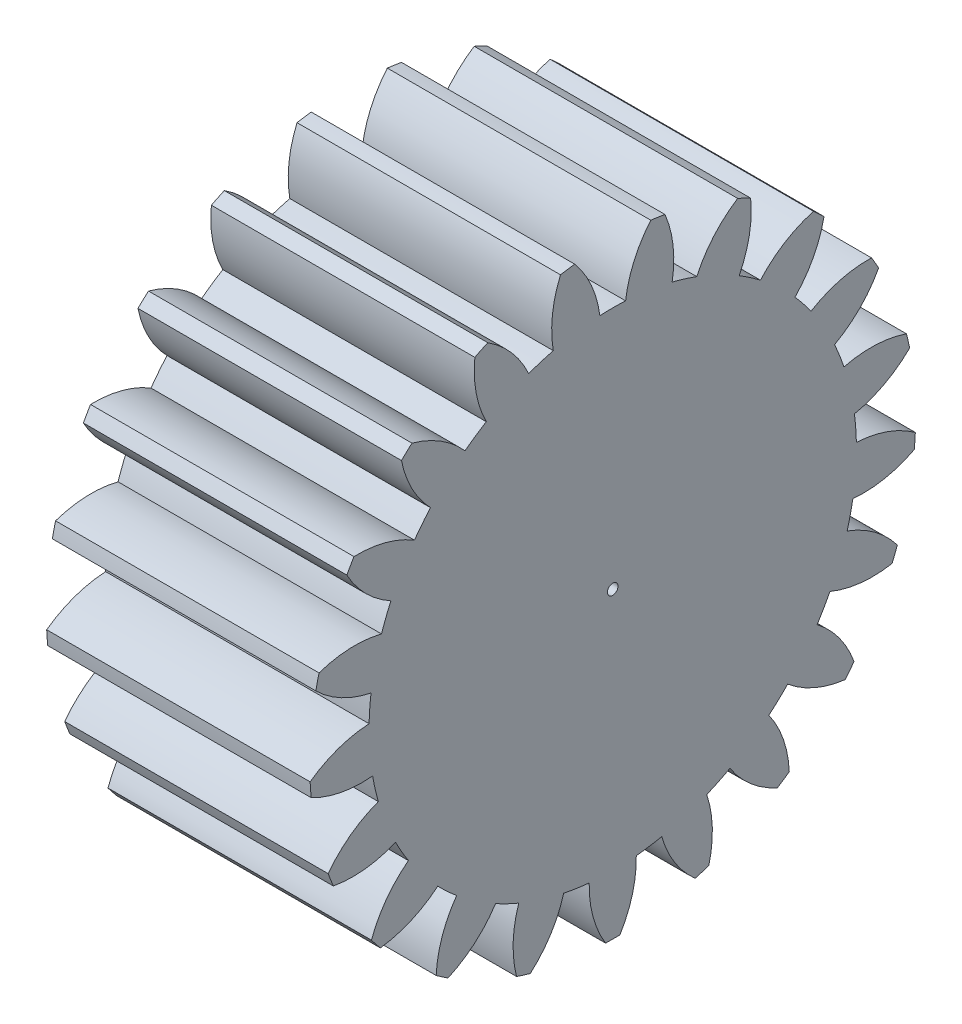
SolidWorks part; units mm, degrees
ref_plane "Plane1" through (0, 0, 0) normal (0, 0, 1) x (1, 0, 0)
ref_plane "Plane2" through (0, 0, 0) normal (0, 1, 0) x (1, 0, 0)
ref_plane "Plane3" through (0, 0, 0) normal (1, 0, 0) x (0, 0, -1)
sketch "HoldingSke" plane through (0, 0, 0) normal (0, 1, 0) x (1, 0, 0)
  line L0 (0, 0) -> (0.4668, -0.1792)
  line L1 (-15, 0) -> (100, 0) construction
  line L2 (0, 0) -> (-2.1039, 2.3779)
  line L3 (0, 0) -> (-11.863, 4.5341)
  line L4 (0, 0) -> (8.0624, 3.0949)
  line L5 (0, 0) -> (-46.8476, -17.4728)
  line L6 (0, 0) -> (-16.5793, -11.1861)
  line L7 (-2.1039, 2.3779) -> (8.6586, 51.2059)
  line L8 (-76.2, 54.61) -> (-76.1, 54.61)
  line L9 (-71.009, 38.7566) -> (-53.1078, 45.2721)
  line L10 (-76.2, 71.12) -> (104.1128, 71.12)
  line L11 (0, 0) -> (-20, 0)
  line L12 (-76.2, 101.6) -> (-76.133, 101.6)
  line L13 (24.9733, 27.94) -> (52.9518, 28.4284)
  line L14 (24.9733, 27.94) -> (24.9743, 27.94)
  line L15 (24.9733, 27.94) -> (100.4006, 29.5858)
  line L16 (-63.627, -2) -> (-12.827, -2)
  circle A0 centre (0, 0) radius 0.4
  circle A1 centre (0, 0) radius 18.499
  circle A2 centre (0, 0) radius 37.5
  circle A3 centre (0, 0) radius 0.4
  dimension "MHD" = 36.998
  dimension "Hub_dia" = 75
  dimension "Bore" = 0.8
  dimension "MBD" = 0.8
  dimension "Num_teeth" = 21
  dimension "Pitch" = 0.5
  dimension "Overall_len" = 50
  dimension "Show_teeth" = 21
  dimension "Thickness" = 20
  dimension "OAL" = 50.0001
  dimension "T_dim" = 0.1
  dimension "Ap" = 20
  dimension "H" = 19.05
  dimension "Pitch_radius" = 180.3128
  dimension "Width" = 20
  dimension "Backlash" = 0.067
  dimension "Addendum_fac" = 1
  dimension "Dedendum_fac" = 1.25
  dimension "Clearance_fac" = 0.25
  dimension "Dedendum_add" = 0.001
  dimension "Module" = 2
sketch "BasProSke" plane through (0, 0, 0) normal (0, 1, 0) x (1, 0, 0)
  line L0 (-10, 0) -> (60, 0) construction
  line L1 (0, 0) -> (0, 23)
  line L2 (0, 0) -> (20, 0)
  line L3 (20, 0) -> (20, 23)
  line L4 (20, 23) -> (0, 23)
  dimension "Thickness" = 20
  dimension "Diameter" = 46
revolve "Base-Revolve" add sketch "BasProSke" angle 360 about L0
sketch "TooCutSke" plane through (0, 0, 0) normal (1, 0, 0) x (0, 0, -1)
  line L1 (0, 0) -> (0, 107) construction
  line L2 (0, 0) -> (-1.6865, 20.9322) construction
  line L3 (0, 0) -> (-6.2448, 41.4315) construction
  line L4 (-1.6865, 20.9322) -> (-3.1224, 20.7157) construction
  arc A0 (0.9768, 18.4732) -> (-0.9768, 18.4732) centre (0, 0) ccw
  arc A1 (2.908, 22.841) -> (-2.908, 22.841) centre (0, 0) ccw
  circle A2 centre (0, 0) radius 21 construction
  circle A3 centre (0, 0) radius 19.7335 construction
  arc A4 (-0.9768, 18.4732) -> (-2.908, 22.841) centre (-9.308, 17.4004) ccw
  arc A5 (2.908, 22.841) -> (0.9768, 18.4732) centre (9.308, 17.4004) ccw
  dimension "Root_dia" = 36.998
  dimension "Overcut_dia" = 46.0508
  dimension "Pitch_dia" = 42
  dimension "Base_dia" = 39.4671
  dimension "Flank_rad" = 8.4
  dimension "Half_ang" = 8.571
  dimension "Half_CT" = 1.4521
extrude "ToothCut" cut sketch "TooCutSke" along normal through all
fillet "Breaks" [suppressed] radius 0.04
fillet "RootFillets" [suppressed] radius 0.501
pattern_circular "TeethCuts" count 21 every 17.143 about axis through (-10, 0, 0) along (1, 0, 0) of "ToothCut", "RootFillets", "Breaks"
sketch "HubNeaOneSke" plane through (0, 0, 0) normal (-1, 0, 0) x (0, 0, 1)
  circle A0 centre (0, 0) radius 18.499
  dimension "Diameter" = 36.998
extrude "HubNearOne" [suppressed] add sketch "HubNeaOneSke" along normal blind 30.0001
sketch "HubNeaBotSke" plane through (0, 0, 0) normal (-1, 0, 0) x (0, 0, 1)
  circle A0 centre (0, 0) radius 18.499
  dimension "Diameter" = 36.998
extrude "HubNearBoth" [suppressed] add sketch "HubNeaBotSke" along normal blind 15
ref_plane "FarPln" through (20, 0, 0) normal (1, 0, 0) x (0, 0, -1)
sketch "HubFarSke" plane through (20, 0, 0) normal (1, 0, 0) x (0, 0, -1)
  circle A0 centre (0, 0) radius 18.499
  dimension "Diameter" = 36.998
extrude "HubFar" [suppressed] add sketch "HubFarSke" along normal blind 15
sketch "BorSke" plane through (0, 0, 0) normal (1, 0, 0) x (0, 0, -1)
  circle A0 centre (0, 0) radius 0.4
  dimension "Diameter" = 0.8
extrude "Bore" cut sketch "BorSke" along normal mid plane 100.0001
sketch "KeySke" plane through (0, 0, 0) normal (1, 0, 0) x (0, 0, -1)
  line L0 (-0.05, 0) -> (-0.05, 0.5)
  line L1 (-0.05, 0.5) -> (0.05, 0.5)
  line L2 (0.05, 0.5) -> (0.05, 0)
  line L3 (0, 0) -> (0, 34) construction
  line L4 (-0.05, 0) -> (0.05, 0)
  dimension "Offset" = 0.5
  dimension "Width" = 0.1
extrude "Keyway" [suppressed] cut sketch "KeySke" along normal mid plane 100.0001
pattern_circular "Keyway2" [suppressed] count 2 every 90 about axis through (-10, 0, 0) along (1, 0, 0)
equation "' \"Module@HoldingSke\" = 6.35"
equation "' \"Num_teeth@HoldingSke\" = 12"
equation "' \"Ap@HoldingSke\" =  20"
equation "' \"Ap@HoldingSke\" = 20"
equation "' \"Width@HoldingSke\" = 0.5 * 25.4"
equation "' \"Hub_dia@HoldingSke\"= 1 * 25.4"
equation "' \"Hub_dia@HoldingSke\" = 1 * 25.4"
equation "' \"Overall_len@HoldingSke\" = 1.0 * 25.4"
equation "' \"Bore@HoldingSke\" = 0.75 * 25.4"
equation "' \"T_dim@HoldingSke\" = 0.1 * 25.4"
equation "' \"Width@KeySke\" = 0.25 * 25.4"
equation "' \"Show_teeth@HoldingSke\" = 13"
equation "' \"Backlash@HoldingSke\" = 0.009 * 25.4"
equation "' \"Addendum_fac@HoldingSke\" = 1.0"
equation "' \"Dedendum_fac@HoldingSke\" = 1.25"
equation "' \"Dedendum_add@HoldingSke\" = 0.00005 * 25.4"
equation "' \"Clearance_fac@HoldingSke\" = 0.25"
equation "\"Pitch@HoldingSke\" = 1 / \"Module@HoldingSke\""
equation "\"Overcut_dia@TooCutSke\" = (\"Num_teeth@HoldingSke\" + 2 * \"Addendum_fac@HoldingSke\") / \"Pitch@HoldingSke\" + 0.002 * 25.4"
equation "\"Pitch_dia@TooCutSke\" = \"Num_teeth@HoldingSke\" / \"Pitch@HoldingSke\""
equation "\"Base_dia@TooCutSke\" = \"Num_teeth@HoldingSke\" / \"Pitch@HoldingSke\" * cos((\"Ap@HoldingSke\"  * 3.14159265 / 180))"
equation "\"Root_dia@TooCutSke\" = (\"Num_teeth@HoldingSke\" + 2) / \"Pitch@HoldingSke\" - 2 * (\"Addendum_fac@HoldingSke\" + \"Dedendum_fac@HoldingSke\") / \"Pitch@HoldingSke\" - \"Dedendum_add@HoldingSke\" * 2"
equation "\"Half_ang@TooCutSke\" = 180 / \"Num_teeth@HoldingSke\""
equation "\"Half_CT@TooCutSke\" = \"Num_teeth@HoldingSke\" / \"Pitch@HoldingSke\" * sin((3.14159265 / 2 / \"Num_teeth@HoldingSke\")) / 2 - 7 * \"Backlash@HoldingSke\" / 4"
equation "\"Flank_rad@TooCutSke\" = \"Num_teeth@HoldingSke\" / \"Pitch@HoldingSke\" / 5"
equation "\"Radius@RootFillets\" = \"Clearance_fac@HoldingSke\" / \"Pitch@HoldingSke\" + \"Dedendum_add@HoldingSke\""
equation "\"Break_rad@Breaks\" = 0.02 / \"Pitch@HoldingSke\""
equation "\"Thickness@HoldingSke\" = \"Width@HoldingSke\""
equation "\"OAL@HoldingSke\" = \"Thickness@HoldingSke\""
equation "\"MHD@HoldingSke\" = (\"Num_teeth@HoldingSke\" + 2) / \"Pitch@HoldingSke\" - 2 * (\"Addendum_fac@HoldingSke\" + \"Dedendum_fac@HoldingSke\")  / \"Pitch@HoldingSke\" - \"Dedendum_add@HoldingSke\" * 2"
equation "\"MBD@HoldingSke\" = (\"Num_teeth@HoldingSke\" + 2) / \"Pitch@HoldingSke\" - 2 * (\"Addendum_fac@HoldingSke\" + \"Dedendum_fac@HoldingSke\")  / \"Pitch@HoldingSke\" - \"Dedendum_add@HoldingSke\" * 2 - 0.002 * 25.4"
equation "\"MHD@HoldingSke\" = ((sgn( \"MHD@HoldingSke\" - \"Hub_dia@HoldingSke\" )-1)*( \"MHD@HoldingSke\" - \"Hub_dia@HoldingSke\" ))/-2+ \"Hub_dia@HoldingSke\""
equation "\"MBD@HoldingSke\" = ((sgn( \"MBD@HoldingSke\" - \"Bore@HoldingSke\" )-1)*( \"MBD@HoldingSke\" - \"Bore@HoldingSke\" ))/-2+ \"Bore@HoldingSke\""
equation "\"OAL@HoldingSke\" = ((sgn( \"OAL@HoldingSke\" - \"Overall_len@HoldingSke\" )+1)*( \"OAL@HoldingSke\" - \"Overall_len@HoldingSke\" ))/2 + \"Overall_len@HoldingSke\" + 0.000002 * 25.4"
equation "\"Num_teeth@TeethCuts\" = int( \"Show_teeth@HoldingSke\" ) + 1"
equation "\"Num_teeth@TeethCuts\" = ((sgn( \"Num_teeth@TeethCuts\" - \"Num_teeth@HoldingSke\" )-1)*( \"Num_teeth@TeethCuts\" - \"Num_teeth@HoldingSke\" ))/-2+ \"Num_teeth@HoldingSke\""
equation "\"Num_teeth@TeethCuts\" = ((sgn( \"Num_teeth@TeethCuts\" - 2.0)+1)*( \"Num_teeth@TeethCuts\" - 2.0))/2 +2.0"
equation "\"Angle@TeethCuts\" = 360.0 / \"Num_teeth@HoldingSke\""
equation "\"Diameter@BasProSke\" = (\"Num_teeth@HoldingSke\" + 2 * \"Addendum_fac@HoldingSke\") / \"Pitch@HoldingSke\""
equation "\"Thickness@BasProSke\"  = \"Thickness@HoldingSke\""
equation "' \"Fillet_rad@BasProSke\" =  \"Thickness@HoldingSke\" * 0.05"
equation "' \"Fillet_rad@BasProSke\" = \"Thickness@HoldingSke\" * 0.05"
equation "\"MHD@HoldingSke\" = ((sgn( \"MHD@HoldingSke\" - \"Root_dia@TooCutSke\" )-1)*( \"MHD@HoldingSke\" - \"Root_dia@TooCutSke\" ))/-2+ \"Root_dia@TooCutSke\""
equation "\"Diameter@HubNeaOneSke\" = \"MHD@HoldingSke\""
equation "\"Length@HubNearOne\" = \"OAL@HoldingSke\" - \"Thickness@BasProSke\""
equation "\"Diameter@HubNeaBotSke\" = \"MHD@HoldingSke\""
equation "\"Length@HubNearBoth\" = ( \"OAL@HoldingSke\" - \"Thickness@BasProSke\" ) / 2.0"
equation "\"Thickness@FarPln\" = \"Thickness@BasProSke\""
equation "\"Diameter@HubFarSke\" = \"MHD@HoldingSke\""
equation "\"Length@HubFar\" = ( \"OAL@HoldingSke\" - \"Thickness@BasProSke\" ) / 2.0"
equation "\"Diameter@BorSke\" = \"MBD@HoldingSke\""
equation "\"D1@Bore\" = \"OAL@HoldingSke\" * 2.0"
equation "\"D1@Keyway\" = \"OAL@HoldingSke\" * 2.0"
equation "\"Offset@KeySke\" = \"T_dim@HoldingSke\" + \"MBD@HoldingSke\" / 2.0"
